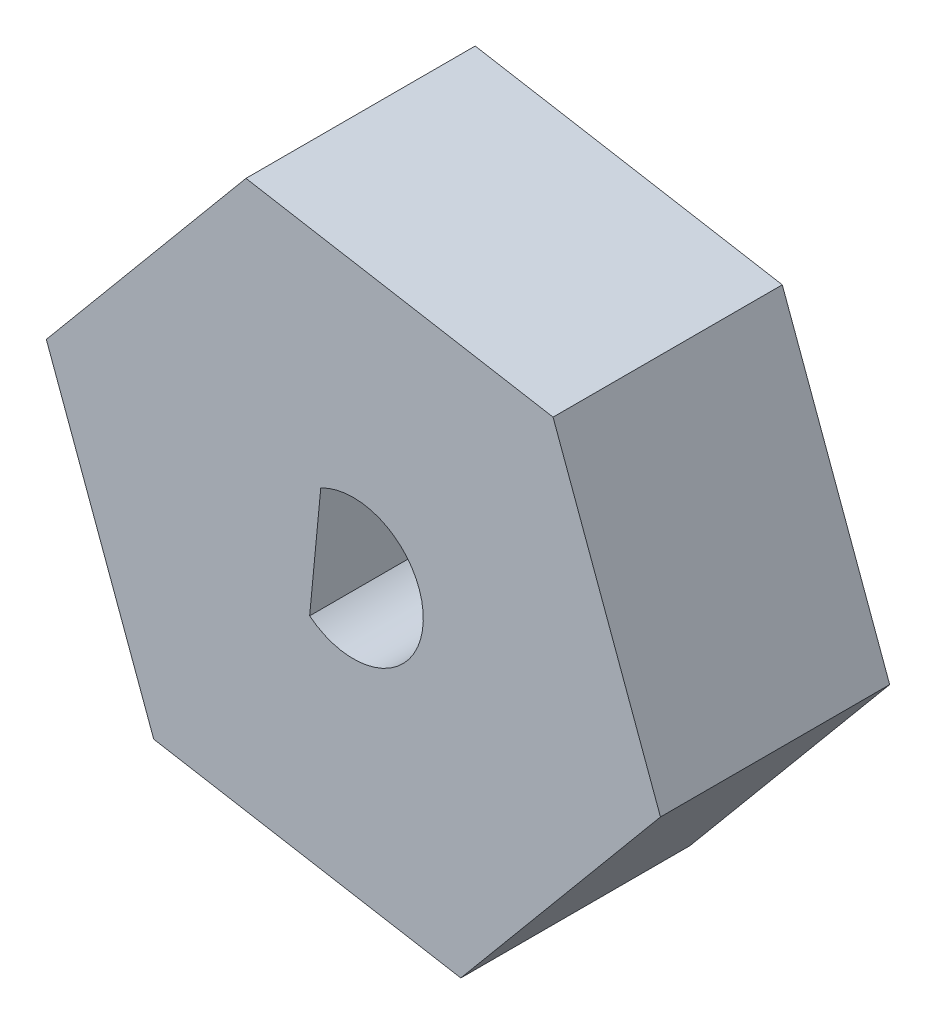
SolidWorks part; units mm, degrees
ref_plane "Front Plane" through (0, 0, 0) normal (0, 0, 1) x (1, 0, 0)
ref_plane "Top Plane" through (0, 0, 0) normal (0, 1, 0) x (1, 0, 0)
ref_plane "Right Plane" through (0, 0, 0) normal (1, 0, 0) x (0, 0, -1)
sketch "Sketch1" plane through (0, 0, 0) normal (0, 0, 1) x (1, 0, 0)
  line L0 (-1.8654, -2.4965) -> (-1.3799, 2.5804)
  line L1 (8.7539, 10.3224) -> (-4.6426, 12.6464)
  line L2 (-4.6426, 12.6464) -> (-13.3534, 2.2066)
  line L3 (-13.3534, 2.2066) -> (-8.6678, -10.5571)
  line L4 (-8.6678, -10.5571) -> (4.7287, -12.881)
  line L5 (4.7287, -12.881) -> (13.4396, -2.4413)
  line L6 (13.4396, -2.4413) -> (8.7539, 10.3224)
  circle A1 centre (0.0431, -0.1173) radius 11.775 construction
  circle A2 centre (0.0431, -0.1173) radius 3.05
  dimension "D4" = 23.55
  dimension "D6" = 6.1
  dimension "D1" = 0
  dimension "D7" = 3.05
  dimension "D8" = 3.05
  dimension "D9" = 5.1
extrude "Boss-Extrude2" add sketch "Sketch1" along normal blind 10
